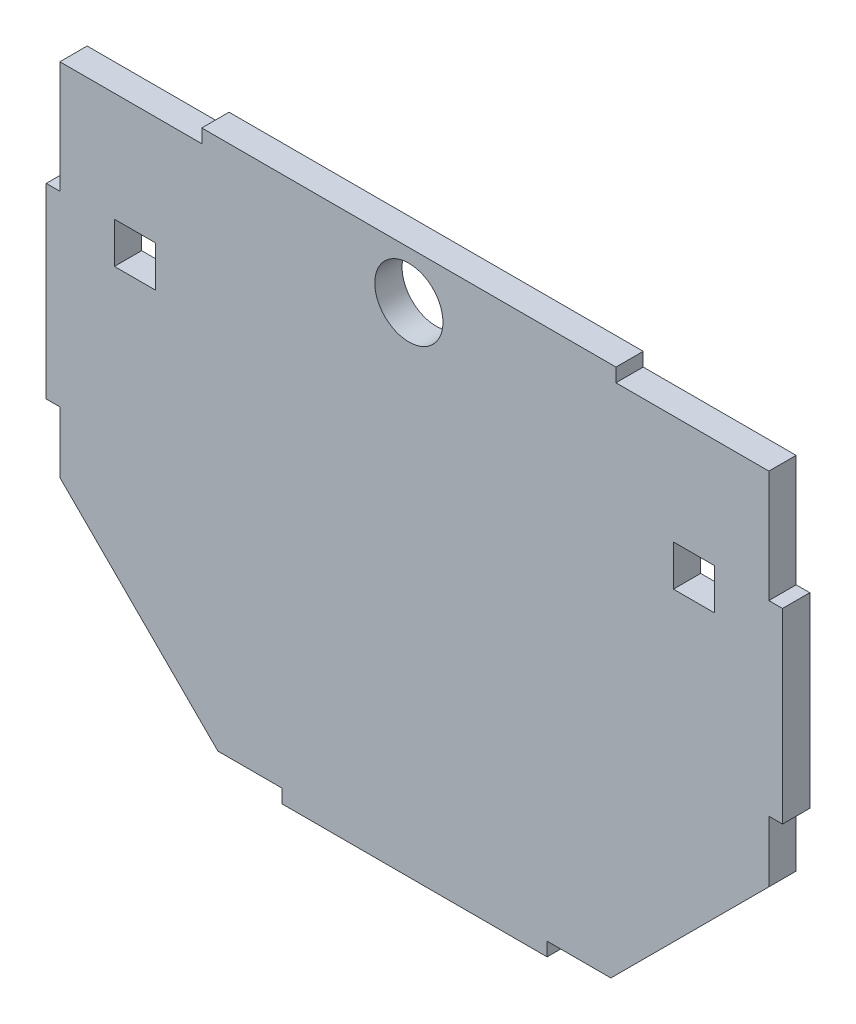
SolidWorks part; units mm, degrees
ref_plane "Front Plane" through (0, 0, 0) normal (0, 0, 1) x (1, 0, 0)
ref_plane "Top Plane" through (0, 0, 0) normal (0, 1, 0) x (1, 0, 0)
ref_plane "Right Plane" through (0, 0, 0) normal (1, 0, 0) x (0, 0, -1)
sketch "Sketch1" plane through (0, 0, 0) normal (0, 0, 1) x (1, 0, 0)
  line L0 (412.0154, 1072.6191) -> (767.6154, 1072.6191) construction
  line L1 (767.6154, 1072.6191) -> (767.6154, 886.9451) construction
  line L2 (767.6154, 886.9451) -> (686.5894, 805.9673) construction
  line L3 (686.5894, 805.9673) -> (493.0414, 805.9673) construction
  line L4 (493.0414, 805.9673) -> (412.0154, 886.9451) construction
  line L5 (412.0154, 886.9451) -> (412.0154, 1072.6191) construction
  line L6 (424.7154, 892.2078) -> (424.7154, 920.7157)
  line L7 (424.7154, 1059.9191) -> (490.8067, 1059.9191)
  line L8 (754.9154, 1059.9191) -> (754.9154, 1007.6919)
  line L9 (754.9154, 892.2078) -> (681.3311, 818.6673)
  line L10 (681.3311, 818.6673) -> (651.6344, 818.6673)
  line L11 (498.2997, 818.6673) -> (424.7154, 892.2078)
  line L21 (424.7154, 1007.6919) -> (424.7154, 1059.9191)
  line L22 (424.7154, 892.2078) -> (424.7154, 1059.9191) construction
  line L23 (754.9154, 920.7157) -> (754.9154, 892.2078)
  line L24 (754.9154, 1059.9191) -> (754.9154, 892.2078) construction
  line L25 (528.0648, 818.6673) -> (498.2997, 818.6673)
  line L26 (681.3311, 818.6673) -> (498.2997, 818.6673) construction
  line L30 (683.7, 1059.9191) -> (754.9154, 1059.9191)
  line L31 (424.7154, 1059.9191) -> (754.9154, 1059.9191) construction
  line L32 (424.7154, 920.7157) -> (418.3654, 920.7157)
  line L33 (418.3654, 920.7157) -> (418.3654, 1007.6919)
  line L34 (418.3654, 1007.6919) -> (424.7154, 1007.6919)
  line L35 (490.8067, 1059.9191) -> (490.8067, 1066.2691)
  line L38 (754.9154, 1007.6919) -> (761.2654, 1007.6919)
  line L39 (761.2654, 1007.6919) -> (761.2654, 920.7157)
  line L40 (761.2654, 920.7157) -> (754.9154, 920.7157)
  line L41 (651.6344, 818.6673) -> (651.6344, 812.3173)
  line L42 (651.6344, 812.3173) -> (528.0648, 812.3173)
  line L43 (528.0648, 812.3173) -> (528.0648, 818.6673)
  line L44 (683.7, 1059.9191) -> (683.7, 1066.2691)
  line L45 (683.7, 1066.2691) -> (490.8067, 1066.2691)
  dimension "D1" = 355.6
  dimension "D2" = 185.674
  dimension "D3" = 114.554
  dimension "D4" = 193.548
  dimension "D6" = 6.35
  dimension "D7" = 6.35
  dimension "D8" = 6.35
  dimension "D9" = 6.35
  dimension "D5" = 12.7
extrude "Boss-Extrude1" add sketch "Sketch1" along normal blind 12.7
sketch "Sketch2" plane through (0, 0, 12.7) normal (0, 0, 1) x (1, 0, 0)
  line L0 (424.7154, 1059.9191) -> (424.7154, 1007.6919) construction
  line L5 (450.1154, 1009.1191) -> (469.1654, 1009.1191)
  line L6 (450.1154, 1009.1191) -> (450.1154, 990.0691)
  line L7 (450.1154, 990.0691) -> (469.1654, 990.0691)
  line L8 (469.1654, 1009.1191) -> (469.1654, 990.0691)
  line L9 (710.4654, 1009.1191) -> (729.5154, 1009.1191)
  line L10 (710.4654, 1009.1191) -> (710.4654, 990.0691)
  line L11 (710.4654, 990.0691) -> (729.5154, 990.0691)
  line L12 (729.5154, 1009.1191) -> (729.5154, 990.0691)
  line L13 (490.8067, 1059.9191) -> (424.7154, 1059.9191) construction
  line L14 (754.9154, 1007.6919) -> (754.9154, 1059.9191) construction
  line L15 (754.9154, 1059.9191) -> (683.7, 1059.9191) construction
  line L16 (490.8067, 1059.9191) -> (683.7, 1059.9191) construction
  circle A0 centre (587.2534, 1044.0441) radius 15.875
  point P22 (0, 0)
  point P23 (587.2534, 1059.9191)
  point P25 (580.2013, 1043.1106)
  point P26 (587.2534, 1059.9191)
  dimension "D6" = 31.75
  dimension "D1" = 25.4
  dimension "D2" = 50.8
  dimension "D3" = 25.4
  dimension "D4" = 50.8
  dimension "D5" = 19.05
  dimension "D7" = 15.875
  dimension "D8" = 0
extrude "Cut-Extrude1" cut sketch "Sketch2" against normal through all
